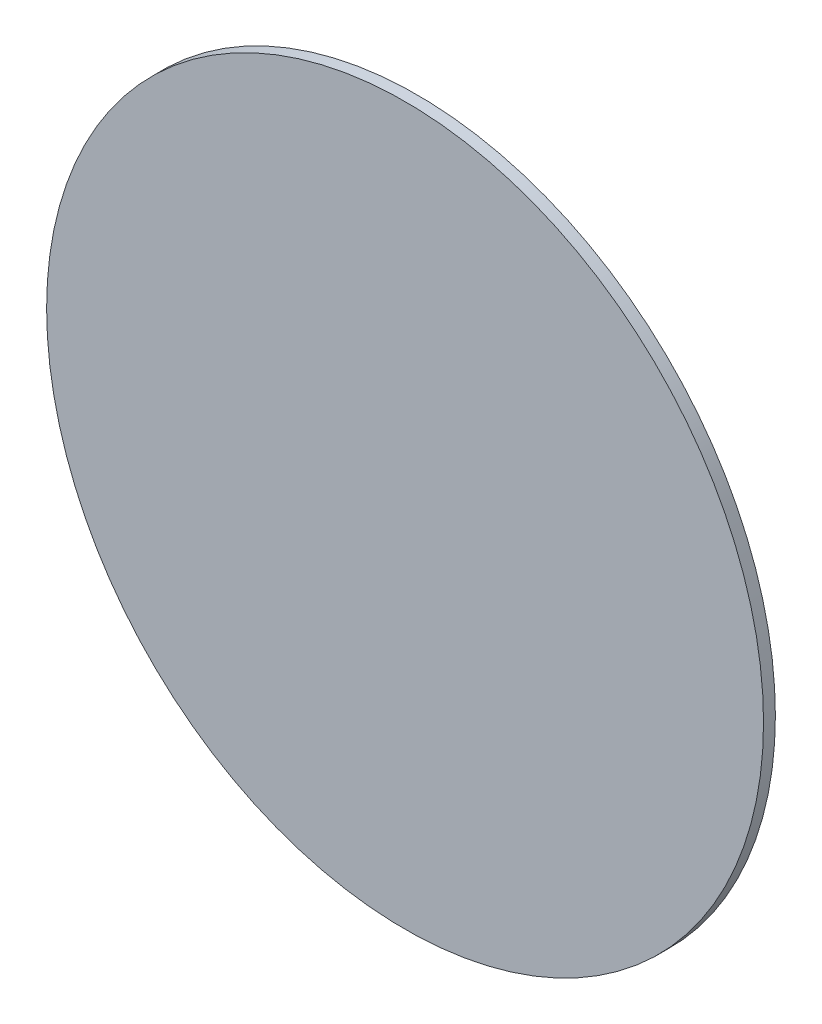
SolidWorks part; units mm, degrees
material "PMMA"
ref_plane "Front Plane" through (0, 0, 0) normal (0, 0, 1) x (1, 0, 0)
ref_plane "Top Plane" through (0, 0, 0) normal (0, 1, 0) x (1, 0, 0)
ref_plane "Right Plane" through (0, 0, 0) normal (1, 0, 0) x (0, 0, -1)
sketch "Sketch1" plane through (0, 0, 0) normal (0, 0, 1) x (1, 0, 0)
  circle A0 centre (0, 0) radius 60.5
  dimension "D1" = 121
extrude "Boss-Extrude1" add sketch "Sketch1" along normal blind 2
